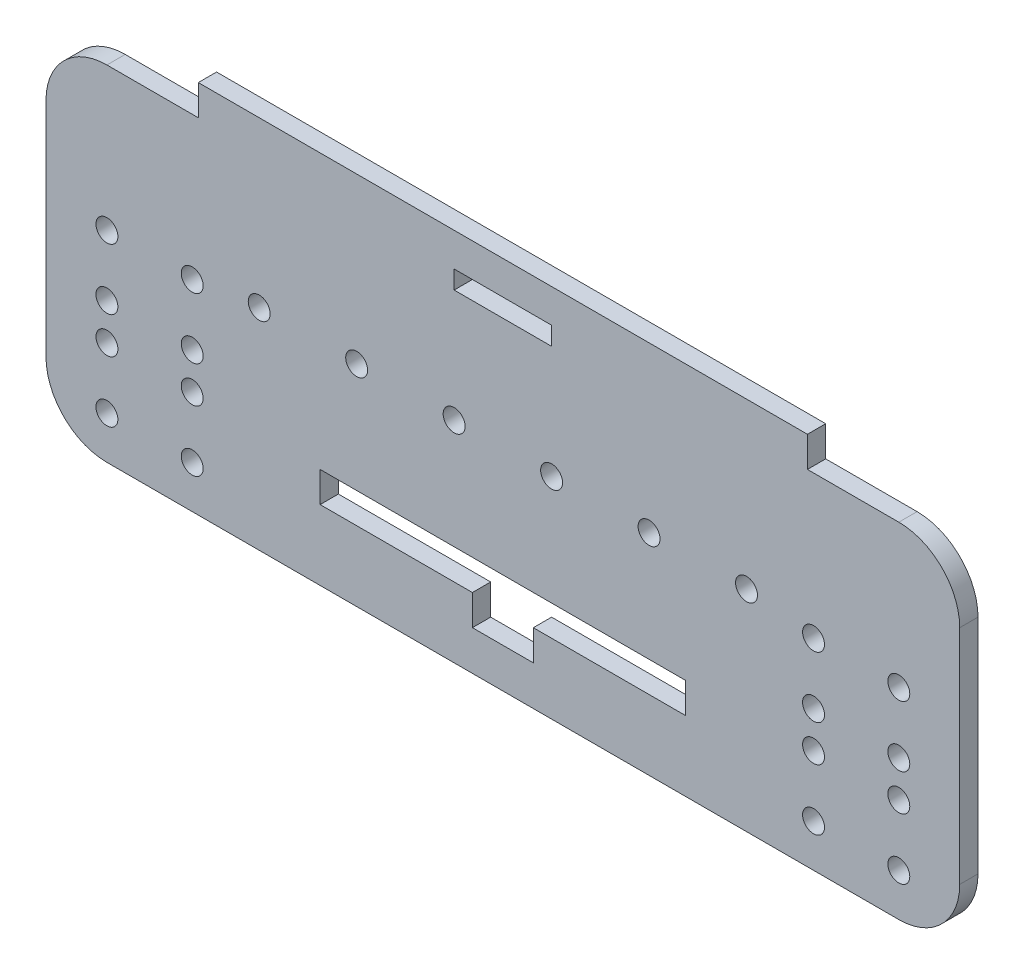
SolidWorks part; units mm, degrees
ref_plane "Front Plane" through (0, 0, 0) normal (0, 0, 1) x (1, 0, 0)
ref_plane "Top Plane" through (0, 0, 0) normal (0, 1, 0) x (1, 0, 0)
ref_plane "Right Plane" through (0, 0, 0) normal (1, 0, 0) x (0, 0, -1)
other "Center of Mass"
sketch "Sketch1" plane through (0, 0, 0) normal (0, 0, 1) x (1, 0, 0)
  line L1 (-65, 28.25) -> (-50, 28.25)
  line L2 (-75, 18.25) -> (-75, -18.25)
  line L3 (-65, -28.25) -> (65, -28.25)
  line L4 (75, 18.25) -> (75, -18.25)
  line L5 (-75, 28.25) -> (75, -28.25) construction
  line L6 (-75, -28.25) -> (75, 28.25) construction
  line L7 (-50, 28.25) -> (-50, 33.25)
  line L8 (-50, 33.25) -> (50, 33.25)
  line L9 (50, 33.25) -> (50, 28.25)
  line L10 (50, 28.25) -> (65, 28.25)
  arc A0 (-75, -18.25) -> (-65, -28.25) centre (-65, -18.25) ccw
  arc A1 (65, -28.25) -> (75, -18.25) centre (65, -18.25) ccw
  arc A2 (65, 28.25) -> (75, 18.25) centre (65, 18.25) cw
  arc A3 (-65, 28.25) -> (-75, 18.25) centre (-65, 18.25) ccw
  point P0 (0, 0)
  dimension "D3" = 10
  dimension "D1" = 56.5
  dimension "D2" = 150
  dimension "D4" = 25
  dimension "D5" = 5
  dimension "D6" = 100
extrude "Boss-Extrude1" add sketch "Sketch1" along normal blind 3
sketch "Sketch2" plane through (0, 0, 3) normal (0, 0, 1) x (1, 0, 0)
  line L0 (0, -11.75) -> (0, 6.25) construction
  line L1 (0, 6.25) -> (8, 6.25) construction
  line L2 (-65, -28.25) -> (-65, -25.25) construction
  line L3 (-65, -25.25) -> (-65, -21.25) construction
  line L4 (-65, -5.25) -> (-65, 4.75) construction
  line L5 (-65, -21.25) -> (-65, -11.25) construction
  line L6 (0, -14.25) -> (75, -14.25) construction
  line L14 (-30, -11.75) -> (30, -11.75)
  line L15 (-30, -11.75) -> (-30, -16.75)
  line L16 (-30, -16.75) -> (30, -16.75)
  line L17 (30, -11.75) -> (30, -16.75)
  line L18 (-30, -11.75) -> (30, -16.75) construction
  line L19 (-30, -16.75) -> (30, -11.75) construction
  line L21 (-65, -11.25) -> (-65, -5.25) construction
  line L22 (-65, 4.75) -> (-51, 4.75) construction
  line L23 (8, 6.25) -> (24, 6.25) construction
  line L24 (24, 6.25) -> (40, 6.25) construction
  line L25 (75, -18.25) -> (75, -14.25) construction
  line L26 (75, -18.25) -> (75, 18.25) construction
  line L27 (0, 6.25) -> (0, 26.25) construction
  line L33 (-8, 27.75) -> (8, 27.75)
  line L34 (-8, 27.75) -> (-8, 24.75)
  line L35 (-8, 24.75) -> (8, 24.75)
  line L36 (8, 27.75) -> (8, 24.75)
  line L37 (-8, 27.75) -> (8, 24.75) construction
  line L38 (-8, 24.75) -> (8, 27.75) construction
  circle A23 centre (-65, -21.25) radius 1.8
  circle A24 centre (-65, -11.25) radius 1.8
  circle A25 centre (-65, -5.25) radius 1.8
  circle A26 centre (-51, -5.25) radius 1.8
  circle A27 centre (-51, -11.25) radius 1.8
  circle A28 centre (-51, -21.25) radius 1.8
  circle A30 centre (51, -5.25) radius 1.8
  circle A31 centre (51, -11.25) radius 1.8
  circle A32 centre (51, -21.25) radius 1.8
  circle A35 centre (65, -21.25) radius 1.8
  circle A36 centre (65, -11.25) radius 1.8
  circle A37 centre (65, -5.25) radius 1.8
  circle A38 centre (-65, 4.75) radius 1.8
  circle A39 centre (-51, 4.75) radius 1.8
  circle A40 centre (65, 4.75) radius 1.8
  circle A41 centre (51, 4.75) radius 1.8
  circle A42 centre (24, 6.25) radius 1.8
  circle A43 centre (40, 6.25) radius 1.8
  circle A44 centre (-40, 6.25) radius 1.8
  circle A45 centre (-24, 6.25) radius 1.8
  circle A46 centre (8, 6.25) radius 1.8
  circle A47 centre (-8, 6.25) radius 1.8
  dimension "D5" = 6
  dimension "D6" = 16
  dimension "D7" = 3.6
  dimension "D8" = 3.6
  dimension "D13" = 3.6
  dimension "D14" = 3.6
  dimension "D18" = 3.6
  dimension "D19" = 3.6
  dimension "D20" = 16
  dimension "D21" = 3.6
  dimension "D22" = 3.6
  dimension "D2" = 3
  dimension "D3" = 4
  dimension "D4" = 10
  dimension "D9" = 5
  dimension "D10" = 60
  dimension "D11" = 18
  dimension "D12" = 8
  dimension "D16" = 10
  dimension "D17" = 14
  dimension "D23" = 75
  dimension "D24" = 4
  dimension "D25" = 20
  dimension "D26" = 3
  dimension "D27" = 16
  dimension "D15" = 2
extrude "Cut-Extrude1" cut sketch "Sketch2" against normal blind 5
sketch "Sketch3" plane through (0, 0, 3) normal (0, 0, 1) x (1, 0, 0)
  line L0 (0, -16.75) -> (0, -19.25) construction
  line L2 (-30, -16.75) -> (30, -16.75) construction
  line L8 (-5, -16.75) -> (5, -16.75)
  line L9 (-5, -16.75) -> (-5, -21.75)
  line L10 (-5, -21.75) -> (5, -21.75)
  line L11 (5, -16.75) -> (5, -21.75)
  line L12 (-5, -16.75) -> (5, -21.75) construction
  line L13 (-5, -21.75) -> (5, -16.75) construction
  dimension "D1" = 2.5
  dimension "D2" = 5
  dimension "D3" = 10
extrude "Cut-Extrude2" cut sketch "Sketch3" against normal blind 10
